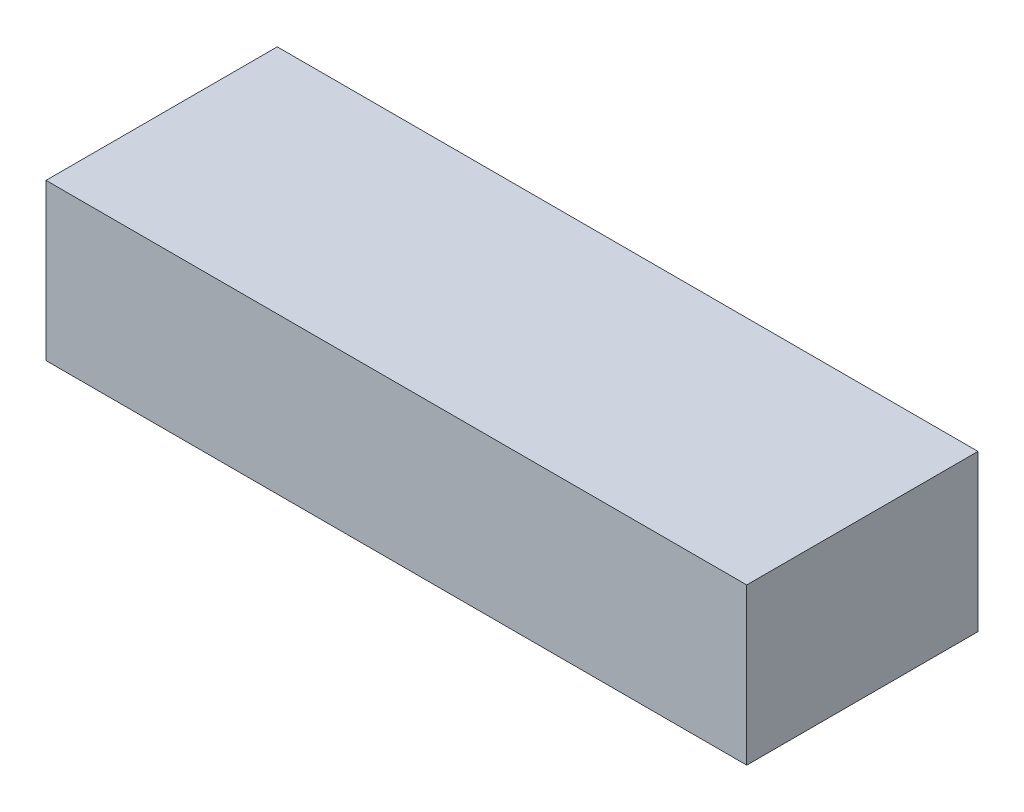
SolidWorks part; units mm, degrees
ref_plane "Front Plane" through (0, 0, 0) normal (0, 0, 1) x (1, 0, 0)
ref_plane "Top Plane" through (0, 0, 0) normal (0, 1, 0) x (1, 0, 0)
ref_plane "Right Plane" through (0, 0, 0) normal (1, 0, 0) x (0, 0, -1)
sketch "Sketch1" plane through (0, 0, 0) normal (0, 1, 0) x (1, 0, 0)
  line L1 (-76.962, -25.4) -> (76.962, -25.4)
  line L2 (-76.962, -25.4) -> (-76.962, 25.4)
  line L3 (-76.962, 25.4) -> (76.962, 25.4)
  line L4 (76.962, -25.4) -> (76.962, 25.4)
  line L5 (-76.962, -25.4) -> (76.962, 25.4) construction
  line L6 (-76.962, 25.4) -> (76.962, -25.4) construction
  point P0 (0, 0)
  dimension "D1" = 153.924
  dimension "D2" = 50.8
extrude "Boss-Extrude1" add sketch "Sketch1" along normal blind 34.29
